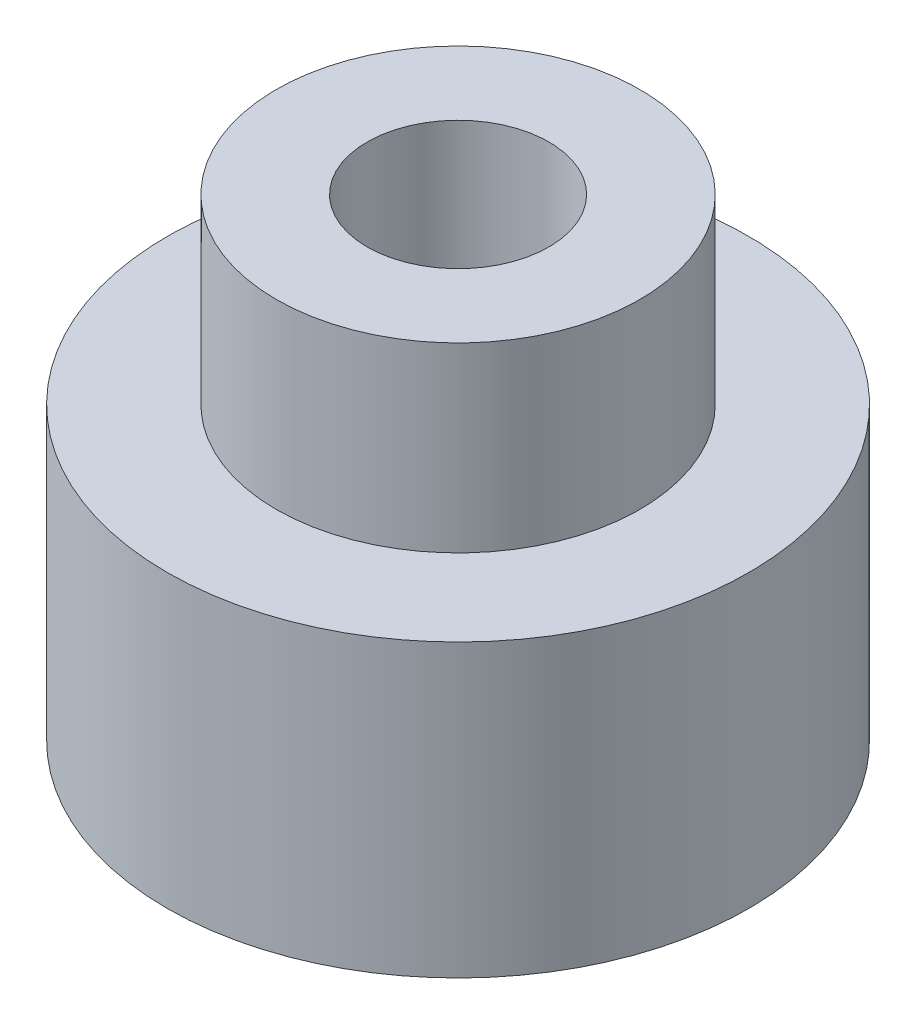
SolidWorks part; units mm, degrees
ref_plane "Plan de face" through (0, 0, 0) normal (0, 0, 1) x (1, 0, 0)
ref_plane "Plan de dessus" through (0, 0, 0) normal (0, 1, 0) x (1, 0, 0)
ref_plane "Plan de droite" through (0, 0, 0) normal (1, 0, 0) x (0, 0, -1)
sketch "Esquisse1" plane through (0, 0, 0) normal (0, 1, 0) x (1, 0, 0)
  circle A0 centre (0, 0) radius 8
  dimension "D1" = 16
extrude "Boss.-Extru.1" add sketch "Esquisse1" along normal blind 8
sketch "Esquisse2" plane through (0, 8, 0) normal (0, 1, 0) x (1, 0, 0)
  circle A0 centre (0, 0) radius 5
  dimension "D1" = 10
extrude "Boss.-Extru.2" add sketch "Esquisse2" along normal blind 5
sketch "Esquisse3" plane through (0, 13, 0) normal (0, 1, 0) x (1, 0, 0)
  circle A0 centre (0, 0) radius 2.5
  dimension "D1" = 5
extrude "Enlèv. mat.-Extru.1" cut sketch "Esquisse3" against normal up to next
